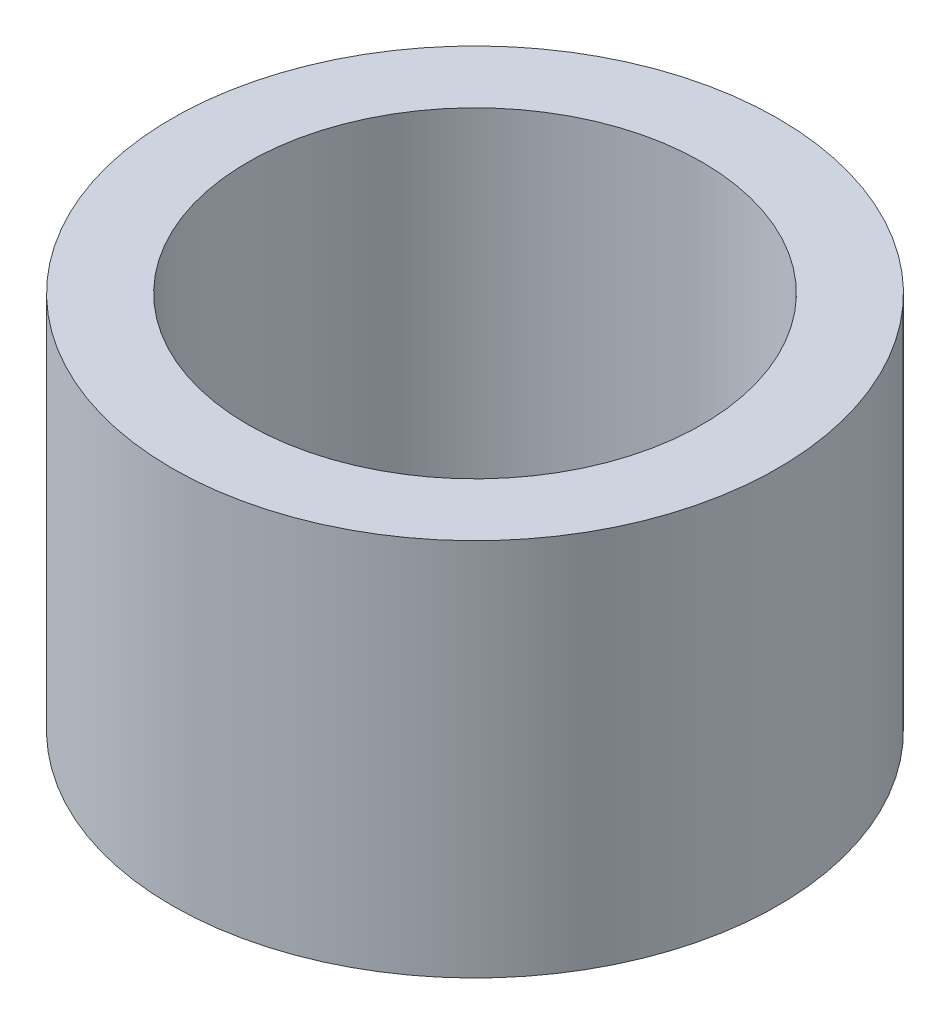
SolidWorks part; units mm, degrees
ref_plane "Front Plane" through (0, 0, 0) normal (0, 0, 1) x (1, 0, 0)
ref_plane "Top Plane" through (0, 0, 0) normal (0, 1, 0) x (1, 0, 0)
ref_plane "Right Plane" through (0, 0, 0) normal (1, 0, 0) x (0, 0, -1)
sketch "Sketch1" plane through (0, 0, 0) normal (0, 1, 0) x (1, 0, 0)
  circle A0 centre (0, 0) radius 4
  circle A1 centre (0, 0) radius 3
  dimension "D1" = 6
  dimension "D2" = 8
extrude "Boss-Extrude1" add sketch "Sketch1" along normal blind 5
